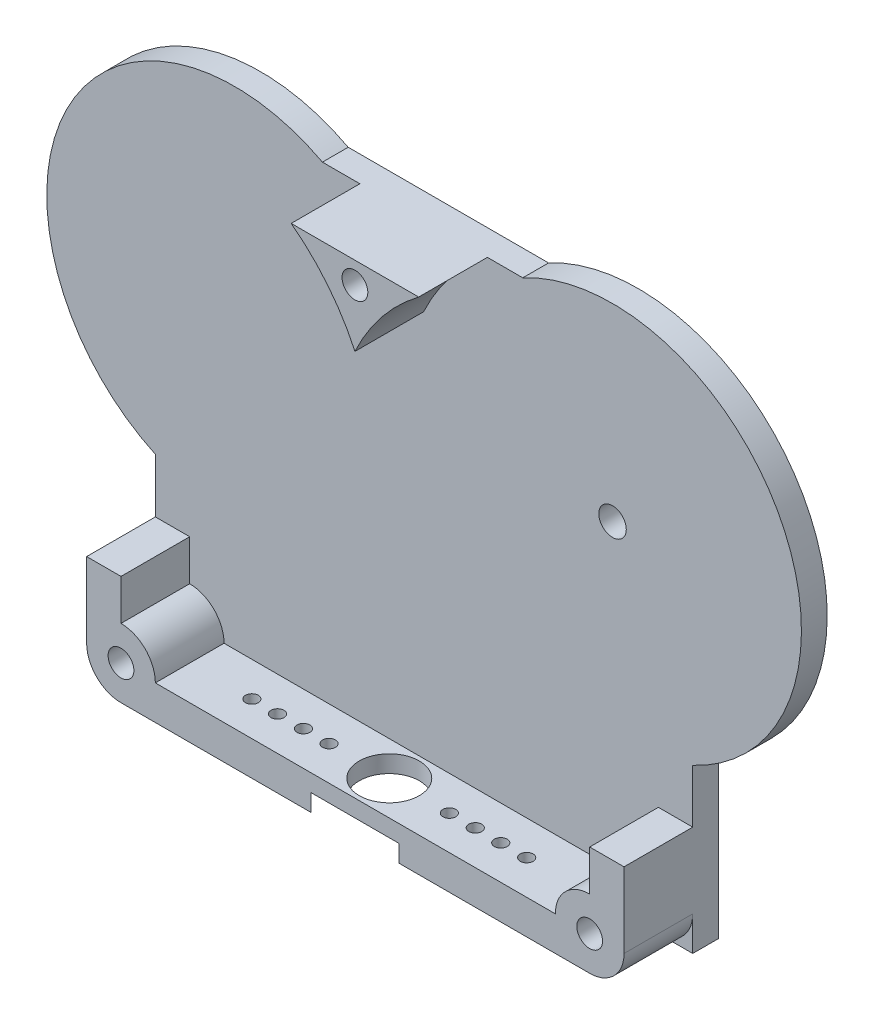
SolidWorks part; units mm, degrees
ref_plane "Alzado" through (0, 0, 0) normal (0, 0, 1) x (1, 0, 0)
ref_plane "Planta" through (0, 0, 0) normal (0, 1, 0) x (1, 0, 0)
ref_plane "Vista lateral" through (0, 0, 0) normal (1, 0, 0) x (0, 0, -1)
sketch "Croquis1" plane through (0, 0, 0) normal (0, 0, 1) x (1, 0, 0)
  line L0 (-41.1649, 0) -> (39.3505, 0) construction
  line L2 (-11.7855, 19.3588) -> (11.6637, 19.3588)
  line L4 (-31.2462, -19.8396) -> (-31.2462, -38.8969)
  line L5 (-31.2462, -38.8969) -> (31.3391, -38.8969)
  line L6 (31.3391, -19.8011) -> (31.3391, -38.8969)
  circle A0 centre (22, 0) radius 1.6
  circle A1 centre (-22, 0) radius 1.6
  arc A2 (-11.7855, 19.3588) -> (-31.2462, -19.8396) centre (-22, 0) ccw
  arc A3 (31.3391, -19.9194) -> (11.5484, 19.3588) centre (22, 0) ccw
  circle A4 centre (-22, 0) radius 22 construction
  circle A5 centre (22, 0) radius 22 construction
  dimension "D1" = 22
  dimension "D2" = 22
extrude "Base Tapa" add sketch "Croquis1" along normal blind 3
sketch "Croquis2" plane through (0, 0, 3) normal (0, 0, 1) x (1, 0, 0)
  line L0 (-11.7855, 19.3588) -> (11.5484, 19.3588) construction
  line L1 (-7.4238, 19.3588) -> (7.4238, 19.3588)
  line L2 (0, -54.4872) -> (0, 39.6411) construction
  line L3 (-76.4701, 0) -> (50.3554, 0) construction
  line L4 (-31.2462, -19.8396) -> (-31.2462, -38.8969) construction
  line L5 (-31.2462, -38.8969) -> (31.3391, -38.8969) construction
  line L6 (31.3391, -19.9194) -> (31.3391, -38.8969) construction
  line L7 (-31.2462, -19.8396) -> (-31.2462, -19.9626)
  line L8 (-27.2462, -38.8969) -> (27.3391, -38.8969)
  line L9 (31.3391, -26.1544) -> (31.3391, -34.8969)
  line L10 (-33.5586, -26.1544) -> (36.6118, -26.1544) construction
  line L11 (-31.2462, -26.1544) -> (-31.2462, -34.8969)
  line L12 (-27.2462, -26.1544) -> (-27.2462, -30.8969)
  line L13 (-23.2462, -34.8969) -> (23.3391, -34.8969)
  line L14 (27.3391, -26.1544) -> (27.3391, -30.8969)
  line L15 (-31.2462, -26.1544) -> (-27.2462, -26.1544)
  line L16 (27.3391, -26.1544) -> (31.3391, -26.1544)
  line L18 (-27.2462, -34.8969) -> (27.3391, -34.8969) construction
  line L19 (-27.2462, -26.1544) -> (-27.2462, -34.8969) construction
  line L20 (-31.2462, -26.1544) -> (-31.2462, -38.8969) construction
  line L21 (-31.2462, -38.8969) -> (31.3391, -38.8969) construction
  line L22 (31.3391, -26.1544) -> (31.3391, -38.8969) construction
  line L23 (27.3391, -26.1544) -> (27.3391, -34.8969) construction
  circle A0 centre (-22, 0) radius 22 construction
  circle A1 centre (22, 0) radius 22 construction
  arc A2 (-7.4238, 19.3588) -> (0, 10.1603) centre (-22, 0) cw
  arc A3 (7.4238, 19.3588) -> (0, 10.1603) centre (22, 0) ccw
  arc A4 (27.3391, -30.8969) -> (23.3391, -34.8969) centre (27.3391, -34.8969) ccw
  arc A5 (-23.2462, -34.8969) -> (-27.2462, -30.8969) centre (-27.2462, -34.8969) ccw
  circle A6 centre (27.3391, -34.8969) radius 1.5
  circle A7 centre (-27.2462, -34.8969) radius 1.5
  arc A8 (-31.2462, -34.8969) -> (-27.2462, -38.8969) centre (-27.2462, -34.8969) ccw
  arc A9 (27.3391, -38.8969) -> (31.3391, -34.8969) centre (27.3391, -34.8969) ccw
  circle A10 centre (0, 16.8576) radius 1.5
  line M1 (31.3391, -38.8969) -> (31.3391, -19.9194)
  line M3 (11.5484, 19.3588) -> (-11.7855, 19.3588)
  line M5 (-31.2462, -19.8396) -> (-31.2462, -38.8969)
  line M6 (-31.2462, -38.8969) -> (31.3391, -38.8969)
extrude "Soportes tapa" add sketch "Croquis2" along normal blind 8 contours A9 L16 L14 A4 L13 A5 L12 L15 A8 A7 A6 M6 M1 M5 | A3 A2 A10 M3
sketch "Croquis3" plane through (0, -34.8969, 0) normal (0, 1, 0) x (1, 0, 0)
  line L0 (-23.2462, -3) -> (23.3391, -3) construction
  line L1 (-23.2462, -11) -> (23.3391, -11) construction
  line L3 (-23.2462, -11) -> (-23.2462, -3) construction
  line L6 (23.3391, -11) -> (23.3391, -3) construction
  line L10 (-23.2462, -3) -> (23.3391, -3) construction
  line L11 (-23.2462, -11) -> (-23.2462, -3) construction
  line L12 (-23.2462, -11) -> (23.3391, -11) construction
  line L13 (23.3391, -11) -> (23.3391, -3) construction
  line L14 (-33.4995, -7) -> (37.0997, -7) construction
  line L15 (0, -14.6579) -> (0, 7.2019) construction
  circle A0 centre (0, -7) radius 3.5
extrude "Caja Horn servo exterior 1" cut sketch "Croquis3" against normal up to surface (4 mm away) up to face at (-0.4536, -38.8969, 5.25)
sketch "Croquis4" plane through (0, -38.8969, 0) normal (0, -1, 0) x (1, 0, 0)
  line L0 (0, 11) -> (0, 3) construction
  line L1 (-28.2323, 7) -> (27.3391, 7) construction
  line L2 (27.3391, 11) -> (27.3391, 3) construction
  line L3 (-16, -1.6138) -> (-16, 13.0641) construction
  line L4 (16, 15.8868) -> (16, 1.3971) construction
  line L5 (-27.8369, 3) -> (27.3391, 3) construction
  line L6 (-11.7855, 3) -> (-43.8884, 3) construction
  line L7 (-27.2462, 11) -> (20.244, 11) construction
  line L8 (-27.2462, 11) -> (27.3391, 11) construction
  line L9 (-16, 9.5) -> (-5.1235, 11)
  line L10 (-16, 4.5) -> (-5.1235, 3)
  line L11 (16, 4.5) -> (5.1235, 3)
  line L12 (16, 9.5) -> (5.1235, 11)
  arc A0 (-5.1235, 3) -> (5.1235, 3) centre (0, 7) ccw
  arc A1 (-16, 9.5) -> (-16, 4.5) centre (-16, 7) ccw
  arc A2 (16, 9.5) -> (16, 4.5) centre (16, 7) cw
  arc A3 (5.1235, 11) -> (-5.1235, 11) centre (0, 7) ccw
  circle A4 centre (-16, 7) radius 0.75
  circle A5 centre (-13, 7.018) radius 0.75
  circle A6 centre (-10.0063, 6.9915) radius 0.75
  circle A7 centre (-7.0063, 7.0095) radius 0.75
  circle A8 centre (7.0063, 7.0095) radius 0.75
  circle A9 centre (10.0063, 6.9915) radius 0.75
  circle A10 centre (13, 7.018) radius 0.75
  circle A11 centre (16, 7) radius 0.75
extrude "Caja Horn servo exterior 2" cut sketch "Croquis4" against normal blind 2
sketch "Croquis5" plane through (0, -38.8969, 0) normal (0, -1, 0) x (1, 0, 0)
  circle A0 centre (-16, 7) radius 0.75 construction
  circle A1 centre (-13, 7.018) radius 0.75 construction
  circle A2 centre (-10.0063, 6.9915) radius 0.75 construction
  circle A3 centre (-7.0063, 7.0095) radius 0.75 construction
  circle A4 centre (7.0063, 7.0095) radius 0.75 construction
  circle A5 centre (10.0063, 6.9915) radius 0.75 construction
  circle A6 centre (13, 7.018) radius 0.75 construction
  circle A7 centre (16, 7) radius 0.75 construction
  circle A8 centre (-16, 7) radius 0.75
  circle A9 centre (-13, 7.018) radius 0.75
  circle A10 centre (-10.0063, 6.9915) radius 0.75
  circle A11 centre (-7.0063, 7.0095) radius 0.75
  circle A12 centre (7.0063, 7.0095) radius 0.75
  circle A13 centre (10.0063, 6.9915) radius 0.75
  circle A14 centre (13, 7.018) radius 0.75
  circle A15 centre (16, 7) radius 0.75
extrude "Taladros Horn servo exterior " cut sketch "Croquis5" against normal up to surface (4 mm away) up to face at (0, -34.8969, 10.5)
sketch "Croquis6" plane through (0, 0, 11) normal (0, 0, 1) x (1, 0, 0)
  circle A0 centre (0, 16.8576) radius 1.5 construction
  circle A1 centre (27.3391, -34.8969) radius 1.5 construction
  circle A2 centre (-27.2462, -34.8969) radius 1.5 construction
  circle A3 centre (0, 16.8576) radius 1.5
  circle A4 centre (27.3391, -34.8969) radius 1.5
  circle A5 centre (-27.2462, -34.8969) radius 1.5
extrude "Taladros Tapa" cut sketch "Croquis6" against normal up to surface (11 mm away) up to face at (0.0104, -9.7803, 0)
sketch "Croquis7" plane through (0, 0, 3) normal (0, 0, 1) x (1, 0, 0)
  circle A0 centre (-22, 0) radius 1.6 construction
  circle A1 centre (-22, 0) radius 1.6
extrude "Rectificar taladro" add sketch "Croquis7" against normal up to surface (3 mm away) up to face at (-25.7462, -34.8969, 0)
chamfer "Chaflán taladros tapa" distance 1 angle 45 3 edges at (28.8391, -34.8969, 0) (-25.7462, -34.8969, 0) (1.5, 16.8576, 0)
